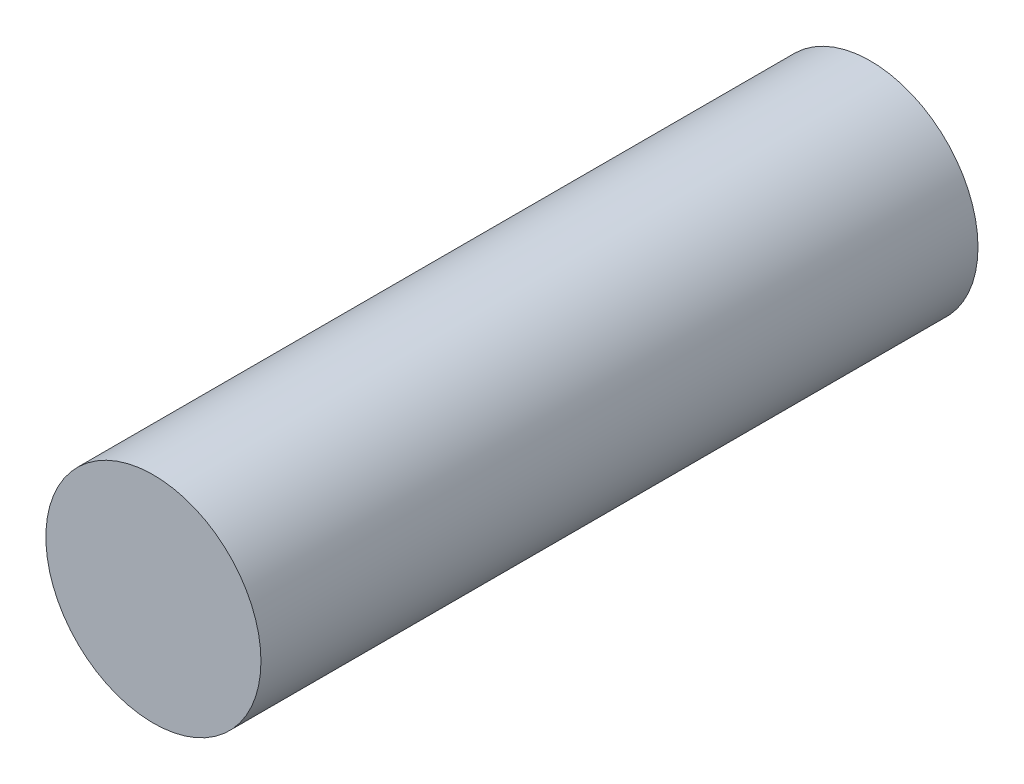
SolidWorks part; units mm, degrees
ref_plane "Front" through (0, 0, 0) normal (0, 0, 1) x (1, 0, 0)
ref_plane "Top" through (0, 0, 0) normal (0, 1, 0) x (1, 0, 0)
ref_plane "Right" through (0, 0, 0) normal (1, 0, 0) x (0, 0, -1)
sketch "Sketch1" plane through (0, 0, 0) normal (0, 0, 1) x (1, 0, 0)
  circle A0 centre (0, 0) radius 7.62
extrude "Base-Extrude" add sketch "Sketch1" along normal blind 50.8
